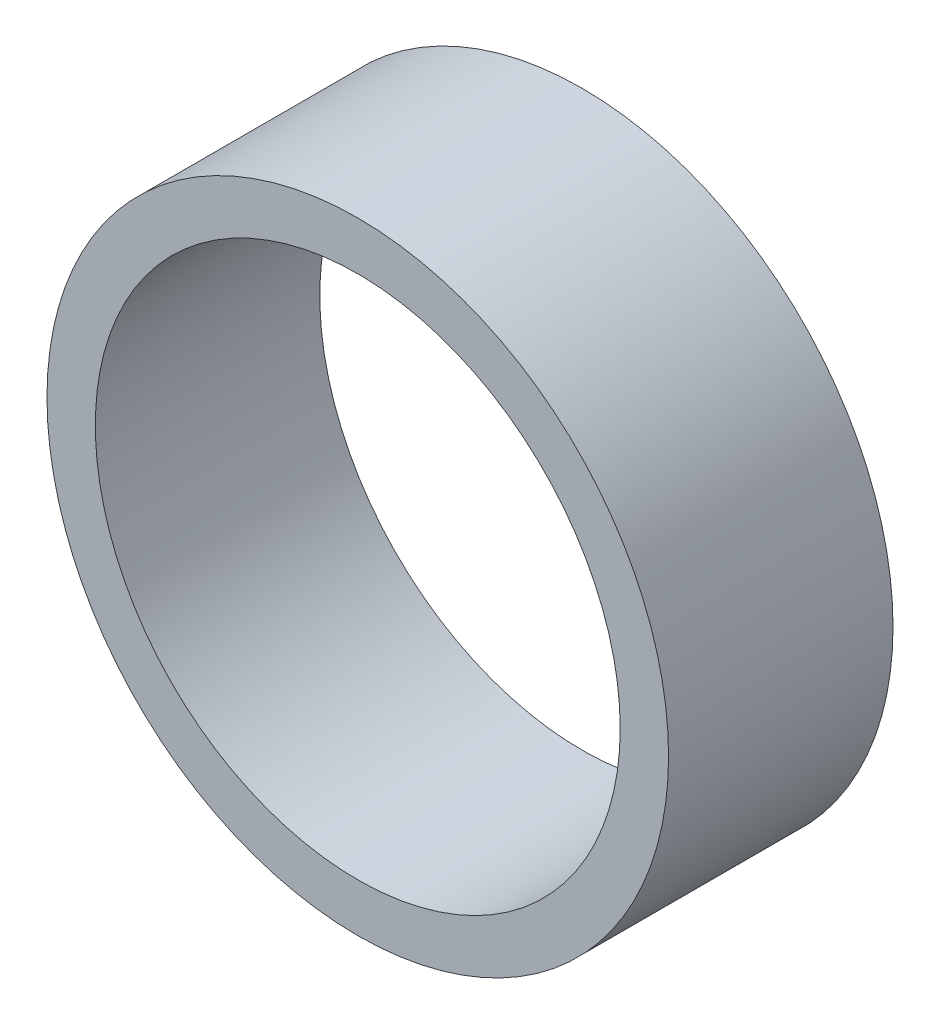
SolidWorks part; units mm, degrees
material "Alumine"
ref_plane "Plan de face" through (0, 0, 0) normal (0, 0, 1) x (1, 0, 0)
ref_plane "Plan de dessus" through (0, 0, 0) normal (0, 1, 0) x (1, 0, 0)
ref_plane "Plan de droite" through (0, 0, 0) normal (1, 0, 0) x (0, 0, -1)
sketch "Esquisse1" plane through (0, 0, 0) normal (0, 0, 1) x (1, 0, 0)
  circle A0 centre (0, 0) radius 9
  circle A1 centre (0, 0) radius 7.6
  dimension "D1" = 15.2
  dimension "D2" = 18
extrude "Boss.-Extru.1" add sketch "Esquisse1" along normal blind 6.5
